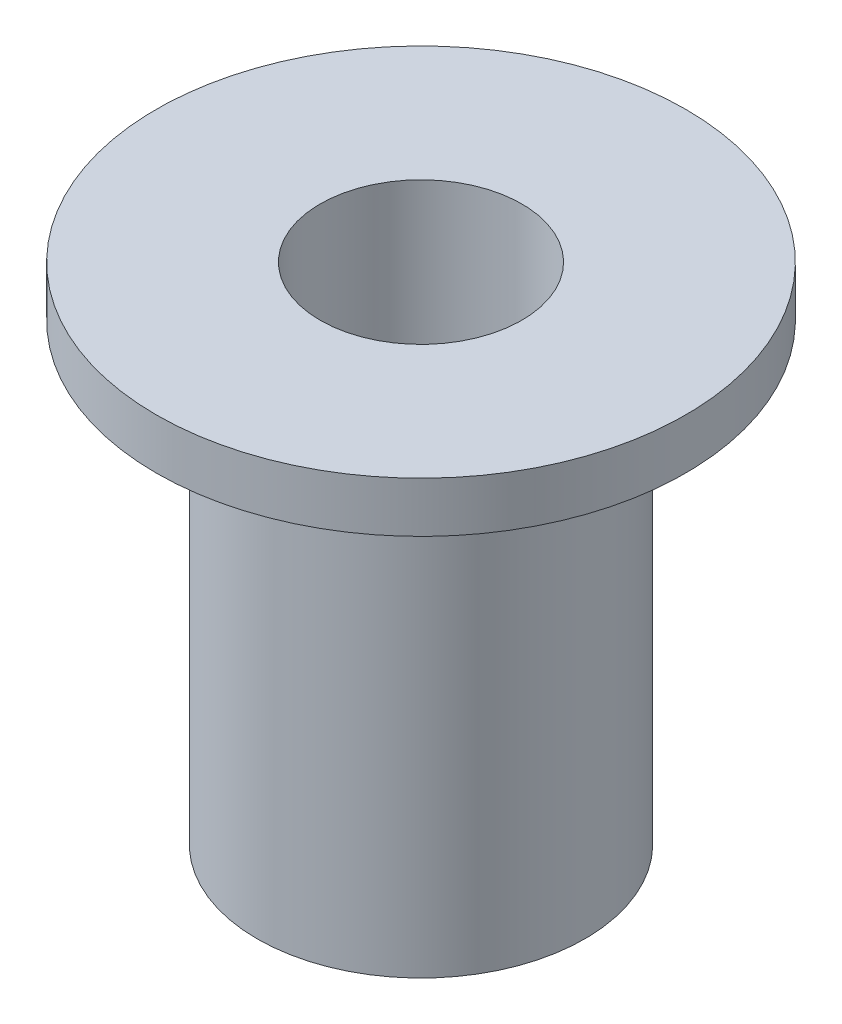
SolidWorks part; units mm, degrees
ref_plane "Front Plane" through (0, 0, 0) normal (0, 0, 1) x (1, 0, 0)
ref_plane "Top Plane" through (0, 0, 0) normal (0, 1, 0) x (1, 0, 0)
ref_plane "Right Plane" through (0, 0, 0) normal (1, 0, 0) x (0, 0, -1)
sketch "Sketch1" plane through (0, 0, 0) normal (0, 1, 0) x (1, 0, 0)
  circle A0 centre (0, 0) radius 6.5
  dimension "D1" = 13
extrude "Boss-Extrude1" add sketch "Sketch1" along normal blind 20
sketch "Sketch2" plane through (0, 20, 0) normal (0, 1, 0) x (1, 0, 0)
  circle A0 centre (0, 0) radius 4
  dimension "D1" = 8
extrude "Cut-Extrude1" cut sketch "Sketch2" against normal offset from surface (16 mm away) 4 up to face at (0, 0, 6.5)
sketch "Sketch3" plane through (0, 4, 0) normal (0, 1, 0) x (1, 0, 0)
  circle A0 centre (0, 0) radius 2
  dimension "D1" = 4
extrude "Cut-Extrude2" cut sketch "Sketch3" against normal through all
sketch "Sketch4" plane through (0, 20, 0) normal (0, 1, 0) x (1, 0, 0)
  circle A0 centre (0, 0) radius 10.5
  circle A1 centre (0, 0) radius 6.5 construction
  circle A2 centre (0, 0) radius 6.5
  dimension "D1" = 4
extrude "Boss-Extrude2" add sketch "Sketch4" against normal blind 2
